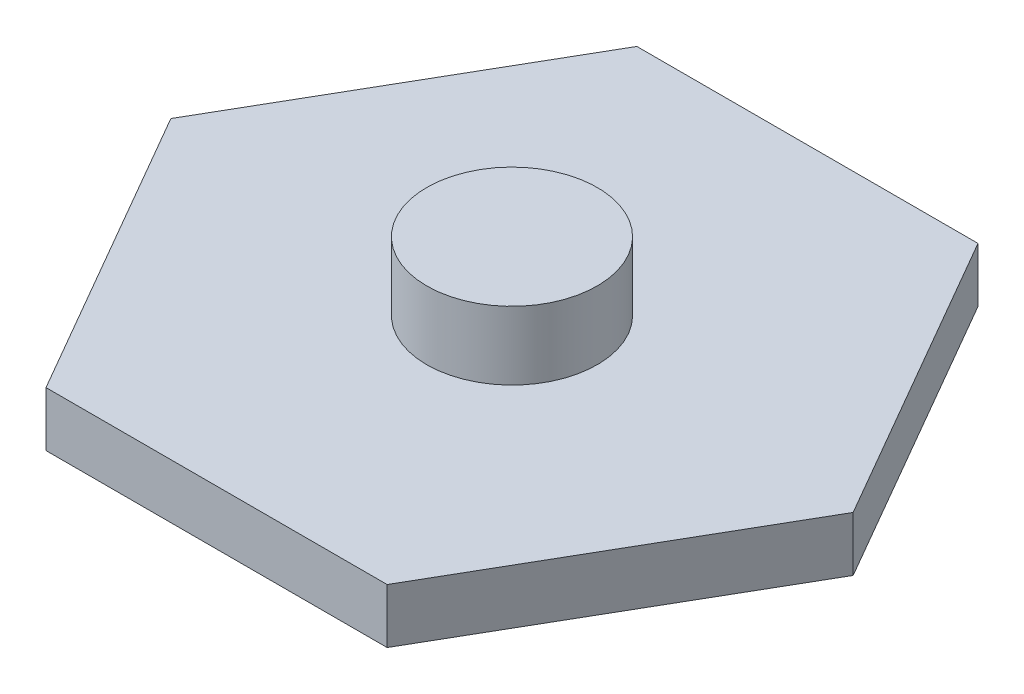
SolidWorks part; units mm, degrees
ref_plane "前视基准面" through (0, 0, 0) normal (0, 0, 1) x (1, 0, 0)
ref_plane "上视基准面" through (0, 0, 0) normal (0, 1, 0) x (1, 0, 0)
ref_plane "右视基准面" through (0, 0, 0) normal (1, 0, 0) x (0, 0, -1)
sketch "草图1" plane through (0, 0, 0) normal (0, 1, 0) x (1, 0, 0)
  line L1 (10, 0) -> (5, 8.6603)
  line L2 (5, 8.6603) -> (-5, 8.6603)
  line L3 (-5, 8.6603) -> (-10, 0)
  line L4 (-10, 0) -> (-5, -8.6603)
  line L5 (-5, -8.6603) -> (5, -8.6603)
  line L6 (5, -8.6603) -> (10, 0)
  circle A0 centre (0, 0) radius 8.6603 construction
  dimension "D1" = 10
extrude "凸台-拉伸1" add sketch "草图1" along normal blind 1.6
sketch "草图2" plane through (0, 1.6, 0) normal (0, 1, 0) x (1, 0, 0)
  circle A0 centre (0, 0) radius 2.5
  dimension "D1" = 5
extrude "凸台-拉伸2" add sketch "草图2" along normal blind 2
